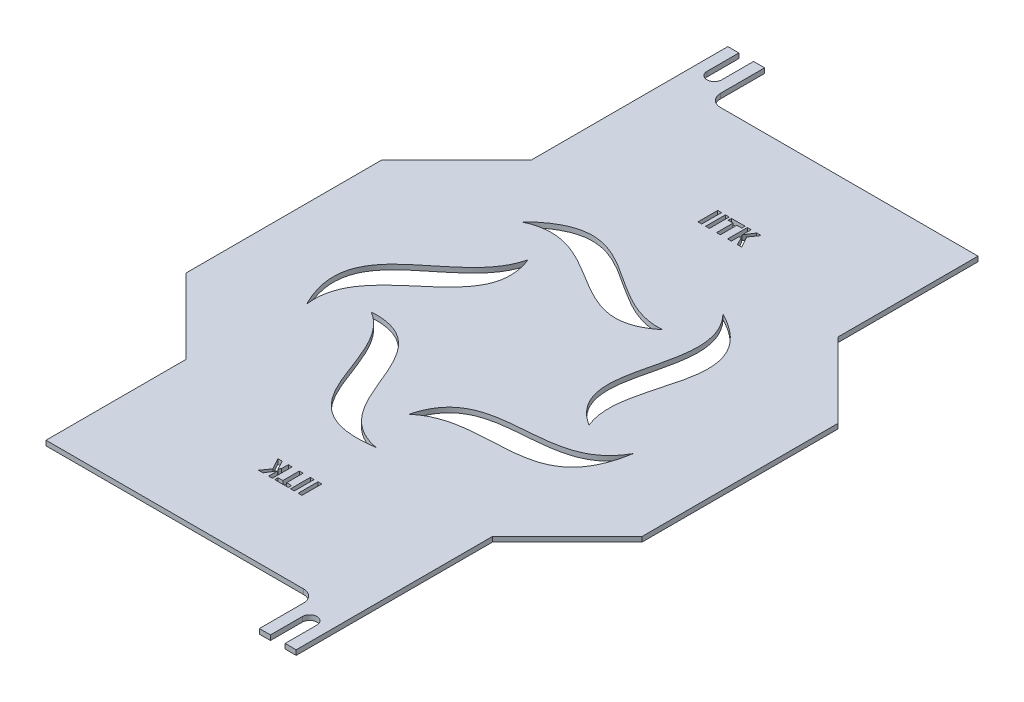
SolidWorks part; units mm, degrees
ref_plane "Front Plane" through (0, 0, 0) normal (0, 0, 1) x (1, 0, 0)
ref_plane "Top Plane" through (0, 0, 0) normal (0, 1, 0) x (1, 0, 0)
ref_plane "Right Plane" through (0, 0, 0) normal (1, 0, 0) x (0, 0, -1)
sketch "Sketch1" plane through (0, 0, 0) normal (0, 1, 0) x (1, 0, 0)
  line L0 (0, 0) -> (0, 150.5) construction
  line L1 (62.5, 150.5) -> (-62.5, 150.5)
  line L2 (-62.5, 150.5) -> (-62.5, 70.5)
  line L3 (-62.5, 70.5) -> (-93, 40)
  line L4 (-93, 40) -> (-93, -40)
  line L5 (0, 0) -> (-93, 0) construction
  line L6 (-62.5, -70.5) -> (-93, -40)
  line L7 (-62.5, -150.5) -> (-62.5, -70.5)
  line L8 (62.5, -150.5) -> (-62.5, -150.5)
  line L9 (62.5, -150.5) -> (62.5, -70.5)
  line L10 (62.5, -70.5) -> (93, -40)
  line L11 (93, 40) -> (93, -40)
  line L12 (62.5, 70.5) -> (93, 40)
  line L13 (62.5, 150.5) -> (62.5, 70.5)
  point P11 (0, -150.5)
  dimension "D1" = 80
  dimension "D2" = 40
extrude "Boss-Extrude1" add sketch "Sketch1" along normal blind 2
sketch "Sketch2" plane through (0, 2, 0) normal (0, 1, 0) x (1, 0, 0)
  line L0 (0, 0) -> (93, 0) construction
  line L1 (93, -40) -> (93, 40) construction
  line L2 (93, 0) -> (0, 0) construction
  line L3 (0, -150.5) -> (0, 150.5) construction
  line L4 (62.5, 150.5) -> (-62.5, 150.5) construction
  line L5 (-3, 150.5) -> (-3, 137.5)
  line L6 (3, 137.5) -> (3, 150.5)
  line L7 (3, 150.5) -> (-3, 150.5)
  line L8 (-3, 137.5) -> (-3, 150.5)
  line L9 (3, 150.5) -> (3, 137.5)
  line L10 (3, -150.5) -> (3, -137.5)
  line L11 (-3, -137.5) -> (-3, -150.5)
  line L12 (3, -150.5) -> (-3, -150.5)
  line L13 (3, -137.5) -> (3, -150.5)
  line L14 (-3, -150.5) -> (-3, -137.5)
  arc A0 (-3, 137.5) -> (3, 137.5) centre (0, 137.5) ccw
  arc A1 (-3, -137.5) -> (3, -137.5) centre (0, -137.5) cw
  line M9 (-62.5, -150.5) -> (62.5, -150.5)
  line M15 (62.5, 150.5) -> (-62.5, 150.5)
  dimension "D2" = 3
  dimension "D1" = 13
extrude "Cut-Extrude1" cut sketch "Sketch2" against normal blind 10 contours L5 A0 L6 M15 | A1 L11 L10 M9
sketch "Sketch3" plane through (0, 2, 0) normal (0, 1, 0) x (1, 0, 0)
  circle A0 centre (0, 0) radius 75 construction
  spline S0 degree 3 poles (61.9353, -12.4807) (48.1881, -37.7648) (10.1523, -13.9307) (2.3401, -44.3064) knots 0 0 0 0 1 1 1 1
  spline S1 degree 3 poles (61.9353, -12.4807) (55.7621, -50.4582) (21.338, -28.075) (2.3401, -44.3064) knots 0 0 0 0 1 1 1 1
  spline S2 degree 3 poles (7.2692, -62.7607) (-21.0256, -57.4996) (-10.1116, -13.9602) (-41.4147, -15.917) knots 0 0 0 0 1 1 1 1
  spline S3 degree 3 poles (7.2692, -62.7607) (-30.7571, -68.6253) (-20.1071, -28.9693) (-41.4147, -15.917) knots 0 0 0 0 1 1 1 1
  spline S4 degree 3 poles (-57.4427, -26.3076) (-61.1826, 2.2281) (-16.4016, 5.3028) (-27.9358, 34.4691) knots 0 0 0 0 1 1 1 1
  spline S5 degree 3 poles (-57.4427, -26.3076) (-74.771, 8.0454) (-33.7649, 10.171) (-27.9358, 34.4691) knots 0 0 0 0 1 1 1 1
  spline S6 degree 3 poles (-42.7708, 46.5017) (-16.7874, 58.8767) (-0.0251, 17.2375) (24.1494, 37.2201) knots 0 0 0 0 1 1 1 1
  spline S7 degree 3 poles (-42.7708, 46.5017) (-15.4539, 73.5976) (-0.7608, 35.2553) (24.1494, 37.2201) knots 0 0 0 0 1 1 1 1
  spline S8 degree 3 poles (31.0089, 55.0473) (50.8075, 34.1597) (16.3861, 5.3506) (42.861, -11.4658) knots 0 0 0 0 1 1 1 1
  spline S9 degree 3 poles (31.0089, 55.0473) (65.22, 37.4405) (33.2947, 11.618) (42.861, -11.4658) knots 0 0 0 0 1 1 1 1
  point P35 (0, 0)
  dimension "D1" = 150
extrude "Cut-Extrude2" cut sketch "Sketch3" against normal blind 10
sketch "Sketch4" plane through (0, 2, 0) normal (0, 1, 0) x (1, 0, 0)
  line L0 (0, -150.5) -> (0, 150.5) construction
  line L1 (0, 150.5) -> (0, -150.5) construction
  line L2 (0, 0) -> (93, 0) construction
  line L3 (93, -40) -> (93, 40) construction
  line L4 (62.5, 150.5) -> (3, 150.5) construction
  line L5 (0, 150.5) -> (44, 150.5)
  line L6 (-31.5, 173.5) -> (-31.5, 127.5)
  line L7 (56.5, 173.5) -> (31.5, 173.5)
  line L8 (56.5, 173.5) -> (56.5, 127.5)
  line L9 (56.5, 127.5) -> (31.5, 127.5)
  line L10 (31.5, 173.5) -> (31.5, 127.5)
  line L11 (56.5, 173.5) -> (31.5, 127.5) construction
  line L12 (56.5, 127.5) -> (31.5, 173.5) construction
  line L13 (-56.5, 173.5) -> (-31.5, 173.5)
  line L14 (-56.5, 173.5) -> (-56.5, 127.5)
  line L15 (-56.5, 127.5) -> (-31.5, 127.5)
  line L16 (56.5, -127.5) -> (31.5, -173.5) construction
  line L17 (56.5, -173.5) -> (31.5, -127.5) construction
  line L18 (-56.5, -127.5) -> (-31.5, -127.5)
  line L19 (-56.5, -173.5) -> (-56.5, -127.5)
  line L20 (-56.5, -173.5) -> (-31.5, -173.5)
  line L21 (31.5, -173.5) -> (31.5, -127.5)
  line L22 (56.5, -127.5) -> (31.5, -127.5)
  line L23 (56.5, -173.5) -> (56.5, -127.5)
  line L24 (56.5, -173.5) -> (31.5, -173.5)
  line L25 (-31.5, -173.5) -> (-31.5, -127.5)
  line L26 (0, -150.5) -> (44, -150.5)
  line M23 (-3, 150.5) -> (-62.5, 150.5)
  line M29 (-62.5, -150.5) -> (-3, -150.5)
  line M33 (3, -150.5) -> (62.5, -150.5)
  line M39 (62.5, 150.5) -> (3, 150.5)
  dimension "D1" = 44
  dimension "D2" = 46
  dimension "D3" = 25
extrude "Cut-Extrude3" cut sketch "Sketch4" against normal blind 10 contours L7 L10 L8 M39 | L10 L9 L8 M39 | L14 L15 L6 M23 | L13 L14 L6 M23 | L20 L25 L19 M29 | L25 L18 L19 M29 | L23 L22 L21 M33 | L24 L23 L21 M33
sketch "Sketch5" plane through (0, 2, 0) normal (0, 1, 0) x (1, 0, 0)
  line L1 (45.049, 173.5) -> (67.951, 173.5)
  line L2 (45.049, 173.5) -> (45.049, 127.5)
  line L3 (45.049, 127.5) -> (67.951, 127.5)
  line L4 (67.951, 173.5) -> (67.951, 127.5)
  line L5 (45.049, 173.5) -> (67.951, 127.5) construction
  line L6 (45.049, 127.5) -> (67.951, 173.5) construction
  line L7 (-31.5, 150.5) -> (-21.5, 150.5)
  line L8 (-31.5, 150.5) -> (-31.5, 127.5)
  line L9 (-31.5, 127.5) -> (-21.5, 127.5)
  line L10 (-21.5, 150.5) -> (-21.5, 127.5)
  point P0 (56.5, 150.5)
  dimension "D1" = 10
extrude "Cut-Extrude4" cut sketch "Sketch5" against normal blind 10
sketch "Sketch6" plane through (0, 2, 0) normal (0, 1, 0) x (1, 0, 0)
  line L1 (-56.5, 150.5) -> (-47.5, 150.5)
  line L2 (-56.5, 150.5) -> (-56.5, 127.5)
  line L3 (-56.5, 127.5) -> (-47.5, 127.5)
  line L4 (-47.5, 150.5) -> (-47.5, 127.5)
  point P7 (0, 0)
  dimension "D1" = 9
extrude "Boss-Extrude2" add sketch "Sketch6" against normal up to surface (2 mm away) up to face at (32.1377, 0, 28.3935)
sketch "Sketch7" plane through (0, 2, 0) normal (0, 1, 0) x (1, 0, 0)
  line L0 (-52, 150.5) -> (-52, 137.5)
  line L1 (-47.5, 150.5) -> (-62.5, 150.5) construction
  line L2 (-58, 137.5) -> (-58, 150.5)
  line L3 (-55, 137.5) -> (-55, 151.8195) construction
  line L4 (-52, 150.5) -> (-58, 150.5)
  arc A0 (-52, 137.5) -> (-58, 137.5) centre (-55, 137.5) cw
  point P10 (-55, 150.5)
  dimension "D1" = 3
  dimension "D2" = 13
extrude "Cut-Extrude5" cut sketch "Sketch7" against normal blind 10
sketch "Sketch8" plane through (0, 2, 0) normal (0, 1, 0) x (1, 0, 0)
  line L0 (31.5, 150.5) -> (3, 150.5) construction
  line L1 (-47.5, 127.5) -> (39.192, 127.5)
  line L2 (-47.5, 127.5) -> (-47.5, 150.5)
  line L3 (-47.5, 150.5) -> (39.192, 150.5)
  line L4 (39.192, 127.5) -> (39.192, 150.5)
extrude "Cut-Extrude6" cut sketch "Sketch8" against normal blind 10
fillet "Fillet1" radius 5 1 edges at (-47.5, 1, -127.5)
mirror "Mirror1" about plane through (0, 0, 0) normal (0, 0, 1) of "Cut-Extrude6"
sketch "Sketch9" plane through (0, 2, 0) normal (0, 1, 0) x (1, 0, 0)
  line L0 (56.5, -127.5) -> (-56.5, -127.5) construction
  line L1 (62.5, -150.5) -> (47.5, -150.5)
  line L2 (62.5, -150.5) -> (62.5, -127.5)
  line L3 (62.5, -127.5) -> (47.5, -127.5)
  line L4 (47.5, -150.5) -> (47.5, -127.5)
  dimension "D1" = 15
extrude "Boss-Extrude3" add sketch "Sketch9" against normal up to surface (2 mm away) up to face at (-42.6893, 0, -4.0808)
sketch "Sketch10" plane through (0, 2, 0) normal (0, 1, 0) x (1, 0, 0)
  line L1 (-56.5, -127.5) -> (-64.6306, -127.5)
  line L2 (-56.5, -127.5) -> (-56.5, -152.7132)
  line L3 (-56.5, -152.7132) -> (-64.6306, -152.7132)
  line L4 (-64.6306, -127.5) -> (-64.6306, -152.7132)
extrude "Cut-Extrude7" cut sketch "Sketch10" against normal blind 10
sketch "Sketch11" plane through (0, 2, 0) normal (0, 1, 0) x (1, 0, 0)
  line L0 (58, -150.5) -> (58, -137.5)
  line L1 (47.5, -150.5) -> (62.5, -150.5) construction
  line L2 (52, -137.5) -> (52, -150.5)
  line L3 (55, -137.5) -> (55, -152.4936) construction
  line L4 (58, -150.5) -> (52, -150.5)
  arc A0 (58, -137.5) -> (52, -137.5) centre (55, -137.5) ccw
  point P6 (55, -150.5)
  dimension "D1" = 6
  dimension "D2" = 13
extrude "Cut-Extrude8" cut sketch "Sketch11" against normal blind 10
fillet "Fillet2" radius 5 1 edges at (47.5, 1, 127.5)
sketch "Sketch12" plane through (0, 2, 0) normal (0, 1, 0) x (1, 0, 0)
  line L0 (46.9585, 82.5) -> (-46.9585, 82.5) construction
  line L1 (0, 127.5) -> (0, 0) construction
  line L2 (62.5, 127.5) -> (-42.5, 127.5) construction
  line L3 (-19.8527, -86.7242) -> (19.8527, -86.7242) construction
  text T0 "<b>IITK                </b>" font "Adobe Gothic Std B" height in points 26
  text T1 "<b>IITK     </b>" font "Adobe Gothic Std B" height in points 26
  point P8 (0, -86.7242)
  dimension "D1" = 45
extrude "Cut-Extrude10" cut sketch "Sketch12" against normal blind 10
